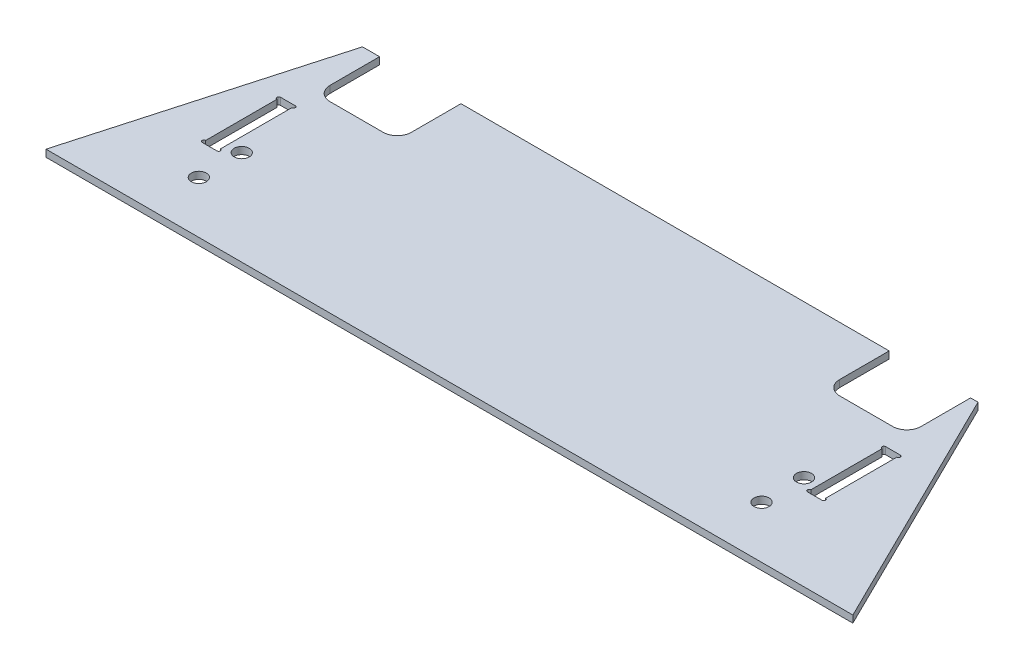
SolidWorks part; units mm, degrees
ref_plane "Front Plane" through (0, 0, 0) normal (0, 0, 1) x (1, 0, 0)
ref_plane "Top Plane" through (0, 0, 0) normal (0, 1, 0) x (1, 0, 0)
ref_plane "Right Plane" through (0, 0, 0) normal (1, 0, 0) x (0, 0, -1)
sketch "Sketch1" plane through (0, 0, 0) normal (0, 1, 0) x (1, 0, 0)
  line L1 (0, 0) -> (361.95, 0)
  line L2 (0, 0) -> (0, 110.744)
  line L3 (0, 110.744) -> (361.95, 110.744)
  line L4 (361.95, 0) -> (361.95, 110.744)
  dimension "D1" = 361.95
  dimension "D2" = 110.744
extrude "Boss-Extrude1" add sketch "Sketch1" along normal blind 3.175
sketch "Sketch2" plane through (0, 3.175, 0) normal (0, 1, 0) x (1, 0, 0)
  line L0 (0, 0) -> (31.233, 110.744)
  line L1 (361.95, 110.744) -> (0, 110.744) construction
  line L2 (31.233, 110.744) -> (0, 110.744)
  line L3 (0, 110.744) -> (0, 0)
  line L5 (361.95, 0) -> (307.3371, 110.744)
  line L6 (307.3371, 110.744) -> (361.95, 110.744)
  line L7 (361.95, 110.744) -> (361.95, 0)
  dimension "D1" = 15.75
  dimension "D2" = 26.25
extrude "Cut-Extrude1" cut sketch "Sketch2" against normal through all
sketch "Sketch3" plane through (0, 3.175, 0) normal (0, 1, 0) x (1, 0, 0)
  line L0 (38.8937, 110.744) -> (38.8937, 82.169)
  line L1 (307.3371, 110.744) -> (31.233, 110.744) construction
  line L2 (38.8937, 82.169) -> (75.4062, 82.169)
  line L3 (75.4062, 82.169) -> (75.4062, 110.744)
  line L4 (75.4062, 110.744) -> (38.8937, 110.744)
  line L5 (267.4937, 110.744) -> (267.4937, 82.169)
  line L6 (267.4937, 82.169) -> (304.0062, 82.169)
  line L7 (304.0062, 82.169) -> (304.0062, 110.744)
  line L8 (304.0062, 110.744) -> (267.4937, 110.744)
  line L9 (40.4812, 248.3207) -> (40.4812, 110.744) construction
  line L10 (73.8187, 248.3207) -> (73.8187, 110.744) construction
  line L11 (269.0812, 248.3207) -> (269.0812, 110.744) construction
  line L13 (302.4187, 248.3207) -> (302.4187, 110.744) construction
  dimension "D1" = 1.5875
  dimension "D2" = 1.5875
  dimension "D3" = 1.5875
  dimension "D4" = 1.5875
  dimension "D5" = 28.575
extrude "Cut-Extrude2" cut sketch "Sketch3" against normal through all
fillet "Fillet1" radius 6.35 4 edges at (304.0062, 1.5875, -82.169) (267.4937, 1.5875, -82.169) (75.4062, 1.5875, -82.169) (38.8937, 1.5875, -82.169)
sketch "Sketch4" plane through (0, 3.175, 0) normal (0, 1, 0) x (1, 0, 0)
  line L0 (57.15, 82.169) -> (57.15, 69.469) construction
  line L1 (45.2437, 82.169) -> (69.0562, 82.169) construction
  line L2 (65.0875, 82.169) -> (65.0875, 69.469)
  line L3 (49.2125, 82.169) -> (49.2125, 69.469)
  line L4 (285.75, 82.169) -> (285.75, 69.469) construction
  line L5 (273.8437, 82.169) -> (297.6562, 82.169) construction
  line L6 (293.6875, 82.169) -> (293.6875, 69.469)
  line L7 (277.8125, 82.169) -> (277.8125, 69.469)
  arc A0 (65.0875, 82.169) -> (49.2125, 82.169) centre (57.15, 82.169) ccw
  arc A1 (49.2125, 69.469) -> (65.0875, 69.469) centre (57.15, 69.469) ccw
  arc A2 (293.6875, 82.169) -> (277.8125, 82.169) centre (285.75, 82.169) ccw
  arc A3 (277.8125, 69.469) -> (293.6875, 69.469) centre (285.75, 69.469) ccw
  point P4 (57.15, 75.819)
  point P9 (285.75, 75.819)
  dimension "D1" = 7.9375
  dimension "D2" = 7.9375
  dimension "D3" = 12.7
  dimension "D4" = 12.7
extrude "Cut-Extrude3" [suppressed] cut sketch "Sketch4" against normal through all
hole_wizard "1/4 Clearance Hole1" positions "Sketch6" profile "Sketch5" hole size "1/4" standard "ANSI Inch" end condition through all
sketch "Sketch6" plane through (0, 3.175, 0) normal (0, 1, 0) x (1, 0, 0)
  point P0 (297.6562, 42.3644)
  point P2 (297.6562, 23.3144)
  point P4 (45.2437, 23.3144)
  point P6 (45.2437, 42.5599)
sketch "Sketch5" plane through (297.6562, 3.175, -42.3644) normal (1, 0, 0) x (0, 0, 1)
  line L0 (0, 0) -> (0, 3.175)
  line L1 (0, 3.175) -> (3.3782, 3.175)
  line L2 (3.3782, 3.175) -> (3.3782, 0)
  line L5 (3.3782, 0) -> (0, 0)
  line L11 (0, -6.35) -> (0, 107.95) construction
  dimension "Thru Hole Dia." = 6.7564
  dimension "Thru Hole Depth" = 3.175
sketch "Sketch7" plane through (0, 3.175, 0) normal (0, 1, 0) x (1, 0, 0)
  line L0 (303.8792, 72.771) -> (303.8792, 37.6534)
  line L1 (32.5437, 72.644) -> (38.8937, 72.644)
  line L2 (32.5437, 72.644) -> (32.5437, 37.7804)
  line L3 (32.5437, 37.7804) -> (38.8937, 37.7804)
  line L4 (38.8937, 72.644) -> (38.8937, 37.7804)
  line L5 (304.0062, 72.644) -> (310.3562, 72.644)
  line L6 (304.0062, 72.644) -> (304.0062, 37.7804)
  line L7 (304.0062, 37.7804) -> (310.3562, 37.7804)
  line L8 (310.3562, 72.644) -> (310.3562, 37.7804)
  line L9 (303.8792, 37.6534) -> (310.4832, 37.6534)
  line L10 (310.4832, 72.771) -> (310.4832, 37.6534)
  line L11 (303.8792, 72.771) -> (310.4832, 72.771)
  line L12 (39.0207, 72.771) -> (39.0207, 37.6534)
  line L13 (32.4167, 37.6534) -> (39.0207, 37.6534)
  line L14 (32.4167, 72.771) -> (32.4167, 37.6534)
  line L15 (32.4167, 72.771) -> (39.0207, 72.771)
  dimension "D1" = 0.127
extrude "Cut-Extrude4" cut sketch "Sketch7" against normal through all
sketch "Sketch8" plane through (0, 3.175, 0) normal (0, 1, 0) x (1, 0, 0)
  line L0 (39.0207, 37.6534) -> (39.0207, 72.771) construction
  line L1 (32.4167, 72.771) -> (32.4167, 37.6534) construction
  line L2 (303.8792, 72.771) -> (303.8792, 37.6534) construction
  line L3 (310.4832, 37.6534) -> (310.4832, 72.771) construction
  circle A0 centre (39.0207, 38.4471) radius 0.7937
  circle A1 centre (39.0207, 71.9772) radius 0.7937
  circle A2 centre (32.4167, 71.9772) radius 0.7937
  circle A3 centre (32.4167, 38.4471) radius 0.7937
  circle A4 centre (303.8792, 71.9772) radius 0.7937
  circle A5 centre (310.4832, 71.9772) radius 0.7937
  circle A6 centre (310.4832, 38.4471) radius 0.7937
  circle A7 centre (303.8792, 38.4471) radius 0.7937
  dimension "D1" = 1.5875
extrude "Cut-Extrude5" cut sketch "Sketch8" against normal through all
